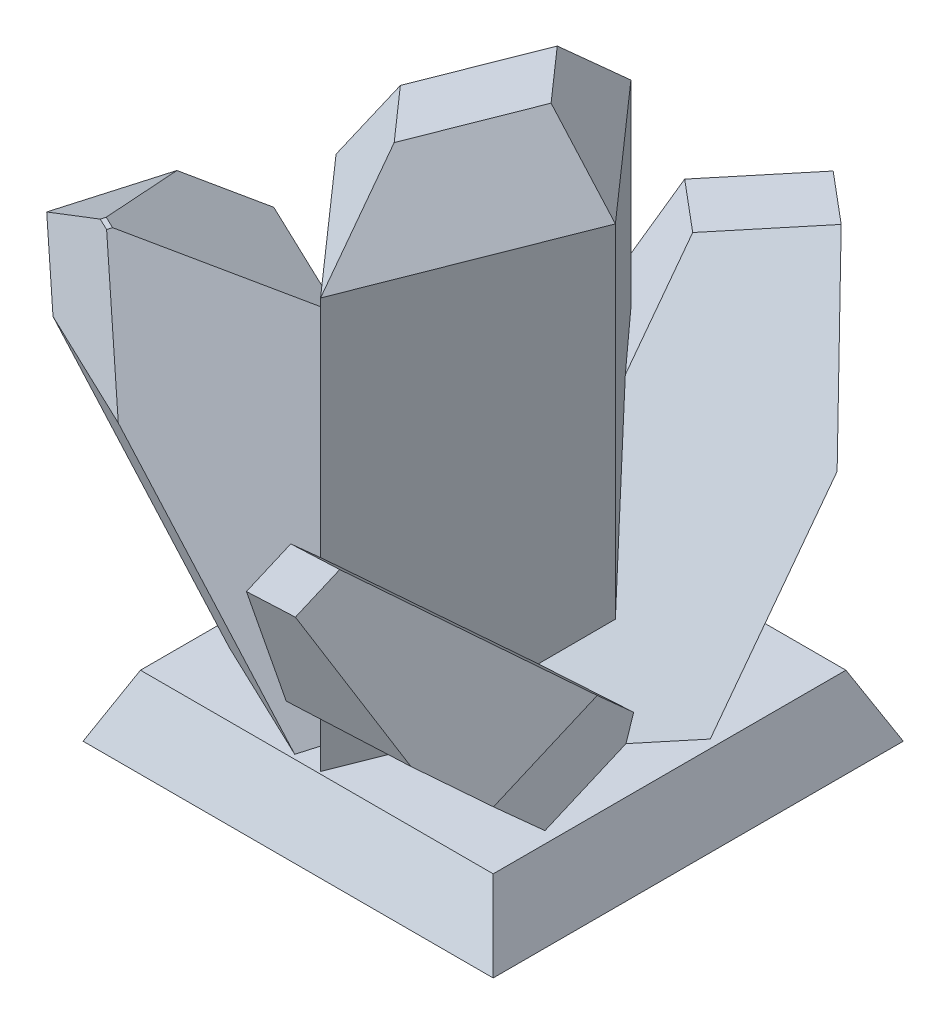
SolidWorks part; units mm, degrees
material "PC High Viscosity"
ref_plane "Front Plane" through (0, 0, 0) normal (0, 0, 1) x (1, 0, 0)
ref_plane "Top Plane" through (0, 0, 0) normal (0, 1, 0) x (1, 0, 0)
ref_plane "Right Plane" through (0, 0, 0) normal (1, 0, 0) x (0, 0, -1)
sketch "Sketch1" plane through (0, 0, 0) normal (0, 1, 0) x (1, 0, 0)
  line L1 (5, -5) -> (-5, -5)
  line L2 (5, -5) -> (5, 5)
  line L3 (5, 5) -> (-5, 5)
  line L4 (-5, -5) -> (-5, 5)
  line L5 (5, -5) -> (-5, 5) construction
  line L6 (5, 5) -> (-5, -5) construction
  point P0 (0, 0)
  dimension "D1" = 10
extrude "Boss-Extrude1" add sketch "Sketch1" along normal blind 1.5 draft 25
sketch "Sketch2" plane through (0, 1.5, 0) normal (0, 1, 0) x (1, 0, 0)
  line L0 (-2.813, -1.018) -> (-0.7831, 4.1416)
  line L1 (-2.813, -1.018) -> (0.0349, -4.245)
  line L2 (-0.7831, 4.1416) -> (2.0649, 0.9146)
  line L3 (0.0349, -4.245) -> (2.0649, 0.9146)
  point P0 (-2.813, -1.018)
extrude "Boss-Extrude2" add sketch "Sketch2" along normal blind 12
chamfer "Chamfer1" distance 2 angle 30 4 edges at (-1.798, 13.5, -1.5618) (-1.389, 13.5, 2.6315) (0.6409, 13.5, -2.5281) (1.0499, 13.5, 1.6652)
sketch "Sketch4" plane through (0, 1.5, 0) normal (0, 1, 0) x (1, 0, 0)
  line L0 (-3.6859, -2.7444) -> (-2.3817, 1.7671)
  line L1 (-3.6859, -2.7444) -> (-0.6429, -4.196)
  line L2 (-2.3817, 1.7671) -> (0.6613, 0.3154)
  line L3 (-0.6429, -4.196) -> (0.6613, 0.3154)
  point P0 (-1.6183, -3.7307)
extrude "Boss-Extrude3" add sketch "Sketch4" along direction (-0.552, 0.8282, 0.0971) on the side of the normal blind 10 contours L0 L2 L3 L1
chamfer "Chamfer2" distance 3 angle 30 3 edges at (-6.3804, 9.7816, -0.0702) (-8.554, 9.7816, 1.4597) (-7.6846, 9.7816, 4.4412)
sketch "Sketch5" plane through (0, 1.5, 0) normal (0, 1, 0) x (1, 0, 0)
  line L0 (-0.7991, 0.6807) -> (0.2887, -2.9366)
  line L1 (-0.7991, 0.6807) -> (2.9321, 0.8605)
  line L2 (0.2887, -2.9366) -> (4.0198, -2.7568)
  line L3 (2.9321, 0.8605) -> (4.0198, -2.7568)
extrude "Boss-Extrude4" add sketch "Sketch5" along direction (0.1285, 0.6705, 0.7307) on the side of the normal blind 8
sketch "Sketch6" plane through (0, 1.5, 0) normal (0, 1, 0) x (1, 0, 0)
  line L0 (-1.6001, 0) -> (1.1808, -2.3374)
  line L1 (-1.6001, 0) -> (1.3196, 3.5298)
  line L2 (1.1808, -2.3374) -> (4.1004, 1.1924)
  line L3 (1.3196, 3.5298) -> (4.1004, 1.1924)
extrude "Boss-Extrude5" add sketch "Sketch6" along direction (0.1285, -0.6705, 0.7307) on the side of the normal blind 10
chamfer "Chamfer3" distance 4 angle 30 4 edges at (-1.4255, 8.2051, -9.0717) (1.4247, 8.2051, -9.6679) (4.5042, 6.8641, 6.7936) (3.1825, 6.8641, 8.6921)
